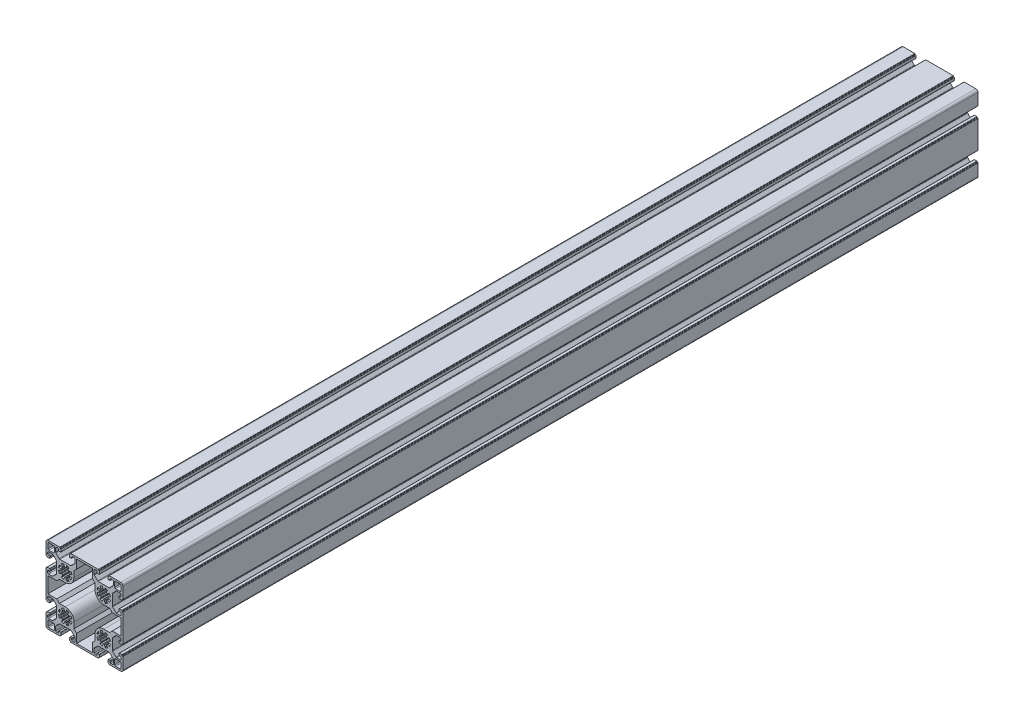
SolidWorks part; units mm, degrees
material "6063 T5"
ref_plane "Спереди" through (0, 0, 0) normal (0, 0, 1) x (1, 0, 0)
ref_plane "Сверху" through (0, 0, 0) normal (0, 1, 0) x (1, 0, 0)
ref_plane "Справа" through (0, 0, 0) normal (1, 0, 0) x (0, 0, -1)
sketch "Эскиз1" plane through (0, 0, 0) normal (0, 0, 1) x (1, 0, 0)
  line L0 (-19.98, 20.5457) -> (20.02, 20.5457) construction
  line L1 (-22.5, 11.25) -> (-22.5, 20)
  line L2 (-20, 22.5) -> (-11.25, 22.5)
  line L3 (65.3, 14) -> (65.3, 19.5)
  line L4 (-13.8, 13) -> (-19.3, 13)
  line L5 (-12.8, 14) -> (-12.8, 19.5)
  line L6 (-13.8, 20.5) -> (-19.3, 20.5)
  line L7 (-20.3, 14) -> (-20.3, 19.5)
  line L8 (0, 0) -> (22.5, 0) construction
  line L13 (0, 0) -> (0, -22.5) construction
  line L14 (0, -22.5) -> (22.5, -22.5) construction
  line L19 (22.5, 0) -> (22.5, -22.5) construction
  line L25 (58.8, 20.5) -> (64.3, 20.5)
  line L26 (-22.5383, 27.0237) -> (22.4617, 27.0237) construction
  line L27 (57.8, 14) -> (57.8, 19.5)
  line L28 (58.8, 13) -> (64.3, 13)
  line L29 (65, 22.5) -> (56.25, 22.5)
  line L30 (67.5, 11.25) -> (67.5, 20)
  line L31 (0, -45) -> (22.5, -45) construction
  line L32 (67.5, -56.25) -> (67.5, -65)
  line L33 (65, -67.5) -> (56.25, -67.5)
  line L34 (58.8, -58) -> (64.3, -58)
  line L35 (57.8, -59) -> (57.8, -64.5)
  line L36 (58.8, -65.5) -> (64.3, -65.5)
  line L37 (-20.3, -59) -> (-20.3, -64.5)
  line L38 (-13.8, -65.5) -> (-19.3, -65.5)
  line L42 (-12.8, -59) -> (-12.8, -64.5)
  line L47 (-13.8, -58) -> (-19.3, -58)
  line L48 (65.3, -59) -> (65.3, -64.5)
  line L49 (-20, -67.5) -> (-11.25, -67.5)
  line L50 (-31.9726, 22.6581) -> (-31.9726, -67.3419) construction
  line L51 (-22.5, -56.25) -> (-22.5, -65)
  line L52 (-22.5, -11.25) -> (-22.5, -33.75)
  line L53 (67.5, -11.25) -> (67.5, -33.75)
  line L55 (11.25, 22.5) -> (33.75, 22.5)
  line L57 (11.25, -67.5) -> (33.75, -67.5)
  line L59 (-22.4849, 32.3089) -> (67.5151, 32.3089) construction
  line L60 (22.5, -22.5) -> (0, 0) construction
  line L61 (-20.3, -31.75) -> (-20.3, -13.25)
  line L62 (-20.3, -13.25) -> (-9.9118, -13.25)
  line L63 (-9.9118, -13.25) -> (-6.8618, -10.2)
  line L64 (-6.8618, -10.2) -> (0, -10.2)
  line L65 (10.2, 6.8618) -> (10.2, 0)
  line L66 (13.25, 9.9118) -> (10.2, 6.8618)
  line L67 (13.25, 20.3) -> (13.25, 9.9118)
  line L68 (31.75, 20.3) -> (13.25, 20.3)
  line L70 (-20.3, -31.75) -> (-9.9118, -31.75)
  line L71 (-9.9118, -31.75) -> (-6.8618, -34.8)
  line L72 (-6.8618, -34.8) -> (0, -34.8)
  line L73 (10.2, -51.8618) -> (10.2, -45)
  line L74 (13.25, -54.9118) -> (10.2, -51.8618)
  line L75 (13.25, -65.3) -> (13.25, -54.9118)
  line L76 (31.75, -65.3) -> (13.25, -65.3)
  line L77 (31.75, 20.3) -> (31.75, 9.9118)
  line L78 (31.75, 9.9118) -> (34.8, 6.8618)
  line L79 (34.8, 6.8618) -> (34.8, 0)
  line L80 (51.8618, -10.2) -> (45, -10.2)
  line L81 (54.9118, -13.25) -> (51.8618, -10.2)
  line L82 (65.3, -13.25) -> (54.9118, -13.25)
  line L83 (65.3, -31.75) -> (65.3, -13.25)
  line L84 (65.3, -31.75) -> (54.9118, -31.75)
  line L85 (54.9118, -31.75) -> (51.8618, -34.8)
  line L86 (51.8618, -34.8) -> (45, -34.8)
  line L87 (34.8, -51.8618) -> (34.8, -45)
  line L88 (31.75, -54.9118) -> (34.8, -51.8618)
  line L89 (31.75, -65.3) -> (31.75, -54.9118)
  arc A0 (-22.5, 20) -> (-20, 22.5) centre (-20, 20) cw
  arc A1 (-19.3, 20.5) -> (-20.3, 19.5) centre (-19.3, 19.5) ccw
  arc A2 (-19.3, 13) -> (-20.3, 14) centre (-19.3, 14) cw
  arc A3 (-13.8, 13) -> (-12.8, 14) centre (-13.8, 14) ccw
  arc A4 (-12.8, 19.5) -> (-13.8, 20.5) centre (-13.8, 19.5) ccw
  arc A5 (57.8, 19.5) -> (58.8, 20.5) centre (58.8, 19.5) cw
  arc A6 (58.8, 13) -> (57.8, 14) centre (58.8, 14) cw
  arc A7 (64.3, 13) -> (65.3, 14) centre (64.3, 14) ccw
  arc A8 (64.3, 20.5) -> (65.3, 19.5) centre (64.3, 19.5) cw
  arc A9 (67.5, 20) -> (65, 22.5) centre (65, 20) ccw
  arc A10 (67.5, -65) -> (65, -67.5) centre (65, -65) cw
  arc A11 (64.3, -65.5) -> (65.3, -64.5) centre (64.3, -64.5) ccw
  arc A12 (64.3, -58) -> (65.3, -59) centre (64.3, -59) cw
  arc A13 (58.8, -58) -> (57.8, -59) centre (58.8, -59) ccw
  arc A14 (57.8, -64.5) -> (58.8, -65.5) centre (58.8, -64.5) ccw
  arc A15 (-12.8, -64.5) -> (-13.8, -65.5) centre (-13.8, -64.5) cw
  arc A16 (-13.8, -58) -> (-12.8, -59) centre (-13.8, -59) cw
  arc A17 (-19.3, -58) -> (-20.3, -59) centre (-19.3, -59) ccw
  arc A18 (-19.3, -65.5) -> (-20.3, -64.5) centre (-19.3, -64.5) cw
  arc A19 (-22.5, -65) -> (-20, -67.5) centre (-20, -65) ccw
  arc A20 (0, -10.2) -> (10.2, 0) centre (0, 0) ccw
  arc A21 (0, -34.8) -> (10.2, -45) centre (0, -45) cw
  arc A22 (45, -10.2) -> (34.8, 0) centre (45, 0) cw
  arc A23 (45, -34.8) -> (34.8, -45) centre (45, -45) ccw
  point P5 (0, 0)
  point P43 (45, 0)
  point P81 (45, -45)
  point P82 (0, -45)
  point P107 (-20.3, -22.5)
  point P120 (22.5, 20.3)
  point P131 (22.5, -65.3)
  line B0 (-22.5, 11.25) -> (-22.5, 6.4)
  line B1 (-22.2, 6.1) -> (-21.8, 6.1)
  line B2 (-21.5, 5.8) -> (-21.5, 5.4)
  line B3 (-21.2, 5.1) -> (-18.3, 5.1)
  line B4 (-18, 5.4) -> (-18, 7.3)
  line B5 (-18.3, 7.6) -> (-19.5, 7.6)
  line B6 (-20.5, 8.6) -> (-20.5, 10.25)
  line B7 (-19.5, 11.25) -> (-15.1142, 11.25)
  line B8 (-14.4071, 10.9571) -> (-10.4929, 7.0429)
  line B9 (-10.2, 6.3358) -> (-10.2, -6.3358)
  line B10 (-10.2, 0) -> (-22.5, 0) construction
  line B11 (-14.4071, -10.9571) -> (-10.4929, -7.0429)
  line B12 (-19.5, -11.25) -> (-15.1142, -11.25)
  line B13 (-20.5, -8.6) -> (-20.5, -10.25)
  line B14 (-18.3, -7.6) -> (-19.5, -7.6)
  line B15 (-18, -5.4) -> (-18, -7.3)
  line B16 (-21.2, -5.1) -> (-18.3, -5.1)
  line B17 (-21.5, -5.8) -> (-21.5, -5.4)
  line B18 (-22.2, -6.1) -> (-21.8, -6.1)
  line B19 (-22.5, -11.25) -> (-22.5, -6.4)
  arc B20 (-18, 7.3) -> (-18.3, 7.6) centre (-18.3, 7.3) ccw
  arc B21 (-18.3, 5.1) -> (-18, 5.4) centre (-18.3, 5.4) ccw
  arc B22 (-21.5, 5.4) -> (-21.2, 5.1) centre (-21.2, 5.4) ccw
  arc B23 (-21.8, 6.1) -> (-21.5, 5.8) centre (-21.8, 5.8) cw
  arc B24 (-22.5, 6.4) -> (-22.2, 6.1) centre (-22.2, 6.4) ccw
  arc B25 (-10.4929, 7.0429) -> (-10.2, 6.3358) centre (-11.2, 6.3358) cw
  arc B26 (-15.1142, 11.25) -> (-14.4071, 10.9571) centre (-15.1142, 10.25) cw
  arc B27 (-20.5, 10.25) -> (-19.5, 11.25) centre (-19.5, 10.25) cw
  arc B28 (-19.5, 7.6) -> (-20.5, 8.6) centre (-19.5, 8.6) cw
  arc B29 (-19.5, -7.6) -> (-20.5, -8.6) centre (-19.5, -8.6) ccw
  arc B30 (-20.5, -10.25) -> (-19.5, -11.25) centre (-19.5, -10.25) ccw
  arc B31 (-15.1142, -11.25) -> (-14.4071, -10.9571) centre (-15.1142, -10.25) ccw
  arc B32 (-10.4929, -7.0429) -> (-10.2, -6.3358) centre (-11.2, -6.3358) ccw
  arc B33 (-22.5, -6.4) -> (-22.2, -6.1) centre (-22.2, -6.4) cw
  arc B34 (-21.8, -6.1) -> (-21.5, -5.8) centre (-21.8, -5.8) ccw
  arc B35 (-21.5, -5.4) -> (-21.2, -5.1) centre (-21.2, -5.4) cw
  arc B36 (-18.3, -5.1) -> (-18, -5.4) centre (-18.3, -5.4) cw
  arc B37 (-18, -7.3) -> (-18.3, -7.6) centre (-18.3, -7.3) cw
  line B38 (0, 0) -> (3.6062, 3.6062) construction
  line B39 (1.3637, 7.358) -> (1.0164, 5.4842)
  line B40 (3.1592, 4.5967) -> (4.2386, 6.1672)
  line B41 (0, 0) -> (0, 5.1) construction
  arc B42 (0.478, -5.0776) -> (-0.478, -5.0776) centre (0, 0) cw
  arc B43 (-6.8804, -4.0816) -> (-7.7513, -1.979) centre (0, 0) cw
  arc B44 (3.9283, 3.2524) -> (3.2524, 3.9283) centre (0, 0) ccw
  arc B45 (4.0816, 6.8804) -> (1.979, 7.7513) centre (0, 0) ccw
  arc B46 (0.478, 5.0776) -> (-0.478, 5.0776) centre (0, 0) ccw
  line B47 (-1.3637, 7.358) -> (-1.0164, 5.4842)
  arc B48 (4.0816, -6.8804) -> (1.979, -7.7513) centre (0, 0) cw
  arc B49 (-3.9283, -3.2524) -> (-3.2524, -3.9283) centre (0, 0) ccw
  line B50 (-3.1592, -4.5967) -> (-4.2386, -6.1672)
  line B51 (0, 0) -> (6.3318, 0) construction
  line B52 (4.5967, 3.1592) -> (6.1672, 4.2386)
  line B53 (7.358, 1.3637) -> (5.4842, 1.0164)
  line B54 (-7.358, 1.3637) -> (-5.4842, 1.0164)
  line B55 (-4.5967, 3.1592) -> (-6.1672, 4.2386)
  line B56 (-3.1592, 4.5967) -> (-4.2386, 6.1672)
  line B57 (7.358, -1.3637) -> (5.4842, -1.0164)
  line B58 (4.5967, -3.1592) -> (6.1672, -4.2386)
  line B59 (3.1592, -4.5967) -> (4.2386, -6.1672)
  line B60 (1.3637, -7.358) -> (1.0164, -5.4842)
  line B61 (-1.3637, -7.358) -> (-1.0164, -5.4842)
  line B62 (-4.5967, -3.1592) -> (-6.1672, -4.2386)
  line B63 (-7.358, -1.3637) -> (-5.4842, -1.0164)
  arc B64 (5.0776, 0.478) -> (5.0776, -0.478) centre (0, 0) cw
  arc B65 (6.8804, 4.0816) -> (7.7513, 1.979) centre (0, 0) cw
  arc B66 (-5.0776, 0.478) -> (-5.0776, -0.478) centre (0, 0) ccw
  arc B67 (-6.8804, 4.0816) -> (-7.7513, 1.979) centre (0, 0) ccw
  arc B68 (-3.9283, 3.2524) -> (-3.2524, 3.9283) centre (0, 0) cw
  arc B69 (-4.0816, 6.8804) -> (-1.979, 7.7513) centre (0, 0) cw
  arc B70 (6.8804, -4.0816) -> (7.7513, -1.979) centre (0, 0) ccw
  arc B71 (3.9283, -3.2524) -> (3.2524, -3.9283) centre (0, 0) cw
  arc B72 (-4.0816, -6.8804) -> (-1.979, -7.7513) centre (0, 0) ccw
  arc B73 (5.0776, 0.478) -> (5.4842, 1.0164) centre (5.5754, 0.5248) cw
  arc B74 (5.4842, -1.0164) -> (5.0776, -0.478) centre (5.5754, -0.5248) cw
  arc B75 (7.7513, -1.979) -> (7.358, -1.3637) centre (7.2669, -1.8554) ccw
  arc B76 (6.8804, -4.0816) -> (6.1672, -4.2386) centre (6.4504, -3.8265) cw
  arc B77 (3.9283, -3.2524) -> (4.5967, -3.1592) centre (4.3135, -3.5713) cw
  arc B78 (3.2524, -3.9283) -> (3.1592, -4.5967) centre (3.5713, -4.3135) ccw
  arc B79 (4.0816, -6.8804) -> (4.2386, -6.1672) centre (3.8265, -6.4504) ccw
  arc B80 (1.979, -7.7513) -> (1.3637, -7.358) centre (1.8554, -7.2669) cw
  arc B81 (0.478, -5.0776) -> (1.0164, -5.4842) centre (0.5248, -5.5754) cw
  arc B82 (-0.478, -5.0776) -> (-1.0164, -5.4842) centre (-0.5248, -5.5754) ccw
  arc B83 (-1.979, -7.7513) -> (-1.3637, -7.358) centre (-1.8554, -7.2669) ccw
  arc B84 (-4.0816, -6.8804) -> (-4.2386, -6.1672) centre (-3.8265, -6.4504) cw
  arc B85 (-3.2524, -3.9283) -> (-3.1592, -4.5967) centre (-3.5713, -4.3135) cw
  arc B86 (-3.9283, -3.2524) -> (-4.5967, -3.1592) centre (-4.3135, -3.5713) ccw
  arc B87 (-6.8804, -4.0816) -> (-6.1672, -4.2386) centre (-6.4504, -3.8265) ccw
  arc B88 (-7.7513, -1.979) -> (-7.358, -1.3637) centre (-7.2669, -1.8554) cw
  arc B89 (-5.4842, -1.0164) -> (-5.0776, -0.478) centre (-5.5754, -0.5248) ccw
  arc B90 (-5.0776, 0.478) -> (-5.4842, 1.0164) centre (-5.5754, 0.5248) ccw
  arc B91 (-7.7513, 1.979) -> (-7.358, 1.3637) centre (-7.2669, 1.8554) ccw
  arc B92 (-6.8804, 4.0816) -> (-6.1672, 4.2386) centre (-6.4504, 3.8265) cw
  arc B93 (-3.9283, 3.2524) -> (-4.5967, 3.1592) centre (-4.3135, 3.5713) cw
  arc B94 (-3.2524, 3.9283) -> (-3.1592, 4.5967) centre (-3.5713, 4.3135) ccw
  arc B95 (-4.0816, 6.8804) -> (-4.2386, 6.1672) centre (-3.8265, 6.4504) ccw
  arc B96 (-1.979, 7.7513) -> (-1.3637, 7.358) centre (-1.8554, 7.2669) cw
  arc B97 (-1.0164, 5.4842) -> (-0.478, 5.0776) centre (-0.5248, 5.5754) ccw
  arc B98 (1.0164, 5.4842) -> (0.478, 5.0776) centre (0.5248, 5.5754) cw
  arc B99 (1.3637, 7.358) -> (1.979, 7.7513) centre (1.8554, 7.2669) cw
  arc B100 (4.2386, 6.1672) -> (4.0816, 6.8804) centre (3.8265, 6.4504) ccw
  arc B101 (3.1592, 4.5967) -> (3.2524, 3.9283) centre (3.5713, 4.3135) ccw
  arc B102 (4.5967, 3.1592) -> (3.9283, 3.2524) centre (4.3135, 3.5713) cw
  arc B103 (6.1672, 4.2386) -> (6.8804, 4.0816) centre (6.4504, 3.8265) cw
  arc B104 (7.7513, 1.979) -> (7.358, 1.3637) centre (7.2669, 1.8554) cw
  line B105 (11.25, 22.5) -> (6.4, 22.5)
  line B106 (6.1, 22.2) -> (6.1, 21.8)
  line B107 (5.8, 21.5) -> (5.4, 21.5)
  line B108 (5.1, 21.2) -> (5.1, 18.3)
  line B109 (5.4, 18) -> (7.3, 18)
  line B110 (7.6, 18.3) -> (7.6, 19.5)
  line B111 (8.6, 20.5) -> (10.25, 20.5)
  line B112 (11.25, 19.5) -> (11.25, 15.1142)
  line B113 (10.9571, 14.4071) -> (7.0429, 10.4929)
  line B114 (6.3358, 10.2) -> (-6.3358, 10.2)
  line B115 (0, 10.2) -> (0, 22.5) construction
  line B116 (-10.9571, 14.4071) -> (-7.0429, 10.4929)
  line B117 (-11.25, 19.5) -> (-11.25, 15.1142)
  line B118 (-8.6, 20.5) -> (-10.25, 20.5)
  line B119 (-7.6, 18.3) -> (-7.6, 19.5)
  line B120 (-5.4, 18) -> (-7.3, 18)
  line B121 (-5.1, 21.2) -> (-5.1, 18.3)
  line B122 (-5.8, 21.5) -> (-5.4, 21.5)
  line B123 (-6.1, 22.2) -> (-6.1, 21.8)
  line B124 (-11.25, 22.5) -> (-6.4, 22.5)
  arc B125 (7.3, 18) -> (7.6, 18.3) centre (7.3, 18.3) ccw
  arc B126 (5.1, 18.3) -> (5.4, 18) centre (5.4, 18.3) ccw
  arc B127 (5.4, 21.5) -> (5.1, 21.2) centre (5.4, 21.2) ccw
  arc B128 (6.1, 21.8) -> (5.8, 21.5) centre (5.8, 21.8) cw
  arc B129 (6.4, 22.5) -> (6.1, 22.2) centre (6.4, 22.2) ccw
  arc B130 (7.0429, 10.4929) -> (6.3358, 10.2) centre (6.3358, 11.2) cw
  arc B131 (11.25, 15.1142) -> (10.9571, 14.4071) centre (10.25, 15.1142) cw
  arc B132 (10.25, 20.5) -> (11.25, 19.5) centre (10.25, 19.5) cw
  arc B133 (7.6, 19.5) -> (8.6, 20.5) centre (8.6, 19.5) cw
  arc B134 (-7.6, 19.5) -> (-8.6, 20.5) centre (-8.6, 19.5) ccw
  arc B135 (-10.25, 20.5) -> (-11.25, 19.5) centre (-10.25, 19.5) ccw
  arc B136 (-11.25, 15.1142) -> (-10.9571, 14.4071) centre (-10.25, 15.1142) ccw
  arc B137 (-7.0429, 10.4929) -> (-6.3358, 10.2) centre (-6.3358, 11.2) ccw
  arc B138 (-6.4, 22.5) -> (-6.1, 22.2) centre (-6.4, 22.2) cw
  arc B139 (-6.1, 21.8) -> (-5.8, 21.5) centre (-5.8, 21.8) ccw
  arc B140 (-5.4, 21.5) -> (-5.1, 21.2) centre (-5.4, 21.2) cw
  arc B141 (-5.1, 18.3) -> (-5.4, 18) centre (-5.4, 18.3) cw
  arc B142 (-7.3, 18) -> (-7.6, 18.3) centre (-7.3, 18.3) cw
  line B143 (67.5, 11.25) -> (67.5, 6.4)
  line B144 (67.2, 6.1) -> (66.8, 6.1)
  line B145 (66.5, 5.8) -> (66.5, 5.4)
  line B146 (66.2, 5.1) -> (63.3, 5.1)
  line B147 (63, 5.4) -> (63, 7.3)
  line B148 (63.3, 7.6) -> (64.5, 7.6)
  line B149 (65.5, 8.6) -> (65.5, 10.25)
  line B150 (64.5, 11.25) -> (60.1142, 11.25)
  line B151 (59.4071, 10.9571) -> (55.4929, 7.0429)
  line B152 (55.2, 6.3358) -> (55.2, -6.3358)
  line B153 (55.2, 0) -> (67.5, 0) construction
  line B154 (59.4071, -10.9571) -> (55.4929, -7.0429)
  line B155 (64.5, -11.25) -> (60.1142, -11.25)
  line B156 (65.5, -8.6) -> (65.5, -10.25)
  line B157 (63.3, -7.6) -> (64.5, -7.6)
  line B158 (63, -5.4) -> (63, -7.3)
  line B159 (66.2, -5.1) -> (63.3, -5.1)
  line B160 (66.5, -5.8) -> (66.5, -5.4)
  line B161 (67.2, -6.1) -> (66.8, -6.1)
  line B162 (67.5, -11.25) -> (67.5, -6.4)
  arc B163 (63, 7.3) -> (63.3, 7.6) centre (63.3, 7.3) cw
  arc B164 (63.3, 5.1) -> (63, 5.4) centre (63.3, 5.4) cw
  arc B165 (66.5, 5.4) -> (66.2, 5.1) centre (66.2, 5.4) cw
  arc B166 (66.8, 6.1) -> (66.5, 5.8) centre (66.8, 5.8) ccw
  arc B167 (67.5, 6.4) -> (67.2, 6.1) centre (67.2, 6.4) cw
  arc B168 (55.4929, 7.0429) -> (55.2, 6.3358) centre (56.2, 6.3358) ccw
  arc B169 (60.1142, 11.25) -> (59.4071, 10.9571) centre (60.1142, 10.25) ccw
  arc B170 (65.5, 10.25) -> (64.5, 11.25) centre (64.5, 10.25) ccw
  arc B171 (64.5, 7.6) -> (65.5, 8.6) centre (64.5, 8.6) ccw
  arc B172 (64.5, -7.6) -> (65.5, -8.6) centre (64.5, -8.6) cw
  arc B173 (65.5, -10.25) -> (64.5, -11.25) centre (64.5, -10.25) cw
  arc B174 (60.1142, -11.25) -> (59.4071, -10.9571) centre (60.1142, -10.25) cw
  arc B175 (55.4929, -7.0429) -> (55.2, -6.3358) centre (56.2, -6.3358) cw
  arc B176 (67.5, -6.4) -> (67.2, -6.1) centre (67.2, -6.4) ccw
  arc B177 (66.8, -6.1) -> (66.5, -5.8) centre (66.8, -5.8) cw
  arc B178 (66.5, -5.4) -> (66.2, -5.1) centre (66.2, -5.4) ccw
  arc B179 (63.3, -5.1) -> (63, -5.4) centre (63.3, -5.4) ccw
  arc B180 (63, -7.3) -> (63.3, -7.6) centre (63.3, -7.3) ccw
  line B181 (45, 0) -> (41.3938, 3.6062) construction
  line B182 (43.6363, 7.358) -> (43.9836, 5.4842)
  line B183 (41.8408, 4.5967) -> (40.7614, 6.1672)
  line B184 (45, 0) -> (45, 5.1) construction
  arc B185 (44.522, -5.0776) -> (45.478, -5.0776) centre (45, 0) ccw
  arc B186 (51.8804, -4.0816) -> (52.7513, -1.979) centre (45, 0) ccw
  arc B187 (41.0717, 3.2524) -> (41.7476, 3.9283) centre (45, 0) cw
  arc B188 (40.9184, 6.8804) -> (43.021, 7.7513) centre (45, 0) cw
  arc B189 (44.522, 5.0776) -> (45.478, 5.0776) centre (45, 0) cw
  line B190 (46.3637, 7.358) -> (46.0164, 5.4842)
  arc B191 (40.9184, -6.8804) -> (43.021, -7.7513) centre (45, 0) ccw
  arc B192 (48.9283, -3.2524) -> (48.2524, -3.9283) centre (45, 0) cw
  line B193 (48.1592, -4.5967) -> (49.2386, -6.1672)
  line B194 (45, 0) -> (38.6682, 0) construction
  line B195 (40.4033, 3.1592) -> (38.8328, 4.2386)
  line B196 (37.642, 1.3637) -> (39.5158, 1.0164)
  line B197 (52.358, 1.3637) -> (50.4842, 1.0164)
  line B198 (49.5967, 3.1592) -> (51.1672, 4.2386)
  line B199 (48.1592, 4.5967) -> (49.2386, 6.1672)
  line B200 (37.642, -1.3637) -> (39.5158, -1.0164)
  line B201 (40.4033, -3.1592) -> (38.8328, -4.2386)
  line B202 (41.8408, -4.5967) -> (40.7614, -6.1672)
  line B203 (43.6363, -7.358) -> (43.9836, -5.4842)
  line B204 (46.3637, -7.358) -> (46.0164, -5.4842)
  line B205 (49.5967, -3.1592) -> (51.1672, -4.2386)
  line B206 (52.358, -1.3637) -> (50.4842, -1.0164)
  arc B207 (39.9224, 0.478) -> (39.9224, -0.478) centre (45, 0) ccw
  arc B208 (38.1196, 4.0816) -> (37.2487, 1.979) centre (45, 0) ccw
  arc B209 (50.0776, 0.478) -> (50.0776, -0.478) centre (45, 0) cw
  arc B210 (51.8804, 4.0816) -> (52.7513, 1.979) centre (45, 0) cw
  arc B211 (48.9283, 3.2524) -> (48.2524, 3.9283) centre (45, 0) ccw
  arc B212 (49.0816, 6.8804) -> (46.979, 7.7513) centre (45, 0) ccw
  arc B213 (38.1196, -4.0816) -> (37.2487, -1.979) centre (45, 0) cw
  arc B214 (41.0717, -3.2524) -> (41.7476, -3.9283) centre (45, 0) ccw
  arc B215 (49.0816, -6.8804) -> (46.979, -7.7513) centre (45, 0) cw
  arc B216 (39.9224, 0.478) -> (39.5158, 1.0164) centre (39.4246, 0.5248) ccw
  arc B217 (39.5158, -1.0164) -> (39.9224, -0.478) centre (39.4246, -0.5248) ccw
  arc B218 (37.2487, -1.979) -> (37.642, -1.3637) centre (37.7331, -1.8554) cw
  arc B219 (38.1196, -4.0816) -> (38.8328, -4.2386) centre (38.5496, -3.8265) ccw
  arc B220 (41.0717, -3.2524) -> (40.4033, -3.1592) centre (40.6865, -3.5713) ccw
  arc B221 (41.7476, -3.9283) -> (41.8408, -4.5967) centre (41.4287, -4.3135) cw
  arc B222 (40.9184, -6.8804) -> (40.7614, -6.1672) centre (41.1735, -6.4504) cw
  arc B223 (43.021, -7.7513) -> (43.6363, -7.358) centre (43.1446, -7.2669) ccw
  arc B224 (44.522, -5.0776) -> (43.9836, -5.4842) centre (44.4752, -5.5754) ccw
  arc B225 (45.478, -5.0776) -> (46.0164, -5.4842) centre (45.5248, -5.5754) cw
  arc B226 (46.979, -7.7513) -> (46.3637, -7.358) centre (46.8554, -7.2669) cw
  arc B227 (49.0816, -6.8804) -> (49.2386, -6.1672) centre (48.8265, -6.4504) ccw
  arc B228 (48.2524, -3.9283) -> (48.1592, -4.5967) centre (48.5713, -4.3135) ccw
  arc B229 (48.9283, -3.2524) -> (49.5967, -3.1592) centre (49.3135, -3.5713) cw
  arc B230 (51.8804, -4.0816) -> (51.1672, -4.2386) centre (51.4504, -3.8265) cw
  arc B231 (52.7513, -1.979) -> (52.358, -1.3637) centre (52.2669, -1.8554) ccw
  arc B232 (50.4842, -1.0164) -> (50.0776, -0.478) centre (50.5754, -0.5248) cw
  arc B233 (50.0776, 0.478) -> (50.4842, 1.0164) centre (50.5754, 0.5248) cw
  arc B234 (52.7513, 1.979) -> (52.358, 1.3637) centre (52.2669, 1.8554) cw
  arc B235 (51.8804, 4.0816) -> (51.1672, 4.2386) centre (51.4504, 3.8265) ccw
  arc B236 (48.9283, 3.2524) -> (49.5967, 3.1592) centre (49.3135, 3.5713) ccw
  arc B237 (48.2524, 3.9283) -> (48.1592, 4.5967) centre (48.5713, 4.3135) cw
  arc B238 (49.0816, 6.8804) -> (49.2386, 6.1672) centre (48.8265, 6.4504) cw
  arc B239 (46.979, 7.7513) -> (46.3637, 7.358) centre (46.8554, 7.2669) ccw
  arc B240 (46.0164, 5.4842) -> (45.478, 5.0776) centre (45.5248, 5.5754) cw
  arc B241 (43.9836, 5.4842) -> (44.522, 5.0776) centre (44.4752, 5.5754) ccw
  arc B242 (43.6363, 7.358) -> (43.021, 7.7513) centre (43.1446, 7.2669) ccw
  arc B243 (40.7614, 6.1672) -> (40.9184, 6.8804) centre (41.1735, 6.4504) cw
  arc B244 (41.8408, 4.5967) -> (41.7476, 3.9283) centre (41.4287, 4.3135) cw
  arc B245 (40.4033, 3.1592) -> (41.0717, 3.2524) centre (40.6865, 3.5713) ccw
  arc B246 (38.8328, 4.2386) -> (38.1196, 4.0816) centre (38.5496, 3.8265) ccw
  arc B247 (37.2487, 1.979) -> (37.642, 1.3637) centre (37.7331, 1.8554) ccw
  line B248 (33.75, 22.5) -> (38.6, 22.5)
  line B249 (38.9, 22.2) -> (38.9, 21.8)
  line B250 (39.2, 21.5) -> (39.6, 21.5)
  line B251 (39.9, 21.2) -> (39.9, 18.3)
  line B252 (39.6, 18) -> (37.7, 18)
  line B253 (37.4, 18.3) -> (37.4, 19.5)
  line B254 (36.4, 20.5) -> (34.75, 20.5)
  line B255 (33.75, 19.5) -> (33.75, 15.1142)
  line B256 (34.0429, 14.4071) -> (37.9571, 10.4929)
  line B257 (38.6642, 10.2) -> (51.3358, 10.2)
  line B258 (45, 10.2) -> (45, 22.5) construction
  line B259 (55.9571, 14.4071) -> (52.0429, 10.4929)
  line B260 (56.25, 19.5) -> (56.25, 15.1142)
  line B261 (53.6, 20.5) -> (55.25, 20.5)
  line B262 (52.6, 18.3) -> (52.6, 19.5)
  line B263 (50.4, 18) -> (52.3, 18)
  line B264 (50.1, 21.2) -> (50.1, 18.3)
  line B265 (50.8, 21.5) -> (50.4, 21.5)
  line B266 (51.1, 22.2) -> (51.1, 21.8)
  line B267 (56.25, 22.5) -> (51.4, 22.5)
  arc B268 (37.7, 18) -> (37.4, 18.3) centre (37.7, 18.3) cw
  arc B269 (39.9, 18.3) -> (39.6, 18) centre (39.6, 18.3) cw
  arc B270 (39.6, 21.5) -> (39.9, 21.2) centre (39.6, 21.2) cw
  arc B271 (38.9, 21.8) -> (39.2, 21.5) centre (39.2, 21.8) ccw
  arc B272 (38.6, 22.5) -> (38.9, 22.2) centre (38.6, 22.2) cw
  arc B273 (37.9571, 10.4929) -> (38.6642, 10.2) centre (38.6642, 11.2) ccw
  arc B274 (33.75, 15.1142) -> (34.0429, 14.4071) centre (34.75, 15.1142) ccw
  arc B275 (34.75, 20.5) -> (33.75, 19.5) centre (34.75, 19.5) ccw
  arc B276 (37.4, 19.5) -> (36.4, 20.5) centre (36.4, 19.5) ccw
  arc B277 (52.6, 19.5) -> (53.6, 20.5) centre (53.6, 19.5) cw
  arc B278 (55.25, 20.5) -> (56.25, 19.5) centre (55.25, 19.5) cw
  arc B279 (56.25, 15.1142) -> (55.9571, 14.4071) centre (55.25, 15.1142) cw
  arc B280 (52.0429, 10.4929) -> (51.3358, 10.2) centre (51.3358, 11.2) cw
  arc B281 (51.4, 22.5) -> (51.1, 22.2) centre (51.4, 22.2) ccw
  arc B282 (51.1, 21.8) -> (50.8, 21.5) centre (50.8, 21.8) cw
  arc B283 (50.4, 21.5) -> (50.1, 21.2) centre (50.4, 21.2) ccw
  arc B284 (50.1, 18.3) -> (50.4, 18) centre (50.4, 18.3) ccw
  arc B285 (52.3, 18) -> (52.6, 18.3) centre (52.3, 18.3) ccw
  line B286 (-22.5, -56.25) -> (-22.5, -51.4)
  line B287 (-22.2, -51.1) -> (-21.8, -51.1)
  line B288 (-21.5, -50.8) -> (-21.5, -50.4)
  line B289 (-21.2, -50.1) -> (-18.3, -50.1)
  line B290 (-18, -50.4) -> (-18, -52.3)
  line B291 (-18.3, -52.6) -> (-19.5, -52.6)
  line B292 (-20.5, -53.6) -> (-20.5, -55.25)
  line B293 (-19.5, -56.25) -> (-15.1142, -56.25)
  line B294 (-14.4071, -55.9571) -> (-10.4929, -52.0429)
  line B295 (-10.2, -51.3358) -> (-10.2, -38.6642)
  line B296 (-10.2, -45) -> (-22.5, -45) construction
  line B297 (-14.4071, -34.0429) -> (-10.4929, -37.9571)
  line B298 (-19.5, -33.75) -> (-15.1142, -33.75)
  line B299 (-20.5, -36.4) -> (-20.5, -34.75)
  line B300 (-18.3, -37.4) -> (-19.5, -37.4)
  line B301 (-18, -39.6) -> (-18, -37.7)
  line B302 (-21.2, -39.9) -> (-18.3, -39.9)
  line B303 (-21.5, -39.2) -> (-21.5, -39.6)
  line B304 (-22.2, -38.9) -> (-21.8, -38.9)
  line B305 (-22.5, -33.75) -> (-22.5, -38.6)
  arc B306 (-18, -52.3) -> (-18.3, -52.6) centre (-18.3, -52.3) cw
  arc B307 (-18.3, -50.1) -> (-18, -50.4) centre (-18.3, -50.4) cw
  arc B308 (-21.5, -50.4) -> (-21.2, -50.1) centre (-21.2, -50.4) cw
  arc B309 (-21.8, -51.1) -> (-21.5, -50.8) centre (-21.8, -50.8) ccw
  arc B310 (-22.5, -51.4) -> (-22.2, -51.1) centre (-22.2, -51.4) cw
  arc B311 (-10.4929, -52.0429) -> (-10.2, -51.3358) centre (-11.2, -51.3358) ccw
  arc B312 (-15.1142, -56.25) -> (-14.4071, -55.9571) centre (-15.1142, -55.25) ccw
  arc B313 (-20.5, -55.25) -> (-19.5, -56.25) centre (-19.5, -55.25) ccw
  arc B314 (-19.5, -52.6) -> (-20.5, -53.6) centre (-19.5, -53.6) ccw
  arc B315 (-19.5, -37.4) -> (-20.5, -36.4) centre (-19.5, -36.4) cw
  arc B316 (-20.5, -34.75) -> (-19.5, -33.75) centre (-19.5, -34.75) cw
  arc B317 (-15.1142, -33.75) -> (-14.4071, -34.0429) centre (-15.1142, -34.75) cw
  arc B318 (-10.4929, -37.9571) -> (-10.2, -38.6642) centre (-11.2, -38.6642) cw
  arc B319 (-22.5, -38.6) -> (-22.2, -38.9) centre (-22.2, -38.6) ccw
  arc B320 (-21.8, -38.9) -> (-21.5, -39.2) centre (-21.8, -39.2) cw
  arc B321 (-21.5, -39.6) -> (-21.2, -39.9) centre (-21.2, -39.6) ccw
  arc B322 (-18.3, -39.9) -> (-18, -39.6) centre (-18.3, -39.6) ccw
  arc B323 (-18, -37.7) -> (-18.3, -37.4) centre (-18.3, -37.7) ccw
  line B324 (0, -45) -> (3.6062, -48.6062) construction
  line B325 (1.3637, -52.358) -> (1.0164, -50.4842)
  line B326 (3.1592, -49.5967) -> (4.2386, -51.1672)
  line B327 (0, -45) -> (0, -50.1) construction
  arc B328 (0.478, -39.9224) -> (-0.478, -39.9224) centre (0, -45) ccw
  arc B329 (-6.8804, -40.9184) -> (-7.7513, -43.021) centre (0, -45) ccw
  arc B330 (3.9283, -48.2524) -> (3.2524, -48.9283) centre (0, -45) cw
  arc B331 (4.0816, -51.8804) -> (1.979, -52.7513) centre (0, -45) cw
  arc B332 (0.478, -50.0776) -> (-0.478, -50.0776) centre (0, -45) cw
  line B333 (-1.3637, -52.358) -> (-1.0164, -50.4842)
  arc B334 (4.0816, -38.1196) -> (1.979, -37.2487) centre (0, -45) ccw
  arc B335 (-3.9283, -41.7476) -> (-3.2524, -41.0717) centre (0, -45) cw
  line B336 (-3.1592, -40.4033) -> (-4.2386, -38.8328)
  line B337 (0, -45) -> (6.3318, -45) construction
  line B338 (4.5967, -48.1592) -> (6.1672, -49.2386)
  line B339 (7.358, -46.3637) -> (5.4842, -46.0164)
  line B340 (-7.358, -46.3637) -> (-5.4842, -46.0164)
  line B341 (-4.5967, -48.1592) -> (-6.1672, -49.2386)
  line B342 (-3.1592, -49.5967) -> (-4.2386, -51.1672)
  line B343 (7.358, -43.6363) -> (5.4842, -43.9836)
  line B344 (4.5967, -41.8408) -> (6.1672, -40.7614)
  line B345 (3.1592, -40.4033) -> (4.2386, -38.8328)
  line B346 (1.3637, -37.642) -> (1.0164, -39.5158)
  line B347 (-1.3637, -37.642) -> (-1.0164, -39.5158)
  line B348 (-4.5967, -41.8408) -> (-6.1672, -40.7614)
  line B349 (-7.358, -43.6363) -> (-5.4842, -43.9836)
  arc B350 (5.0776, -45.478) -> (5.0776, -44.522) centre (0, -45) ccw
  arc B351 (6.8804, -49.0816) -> (7.7513, -46.979) centre (0, -45) ccw
  arc B352 (-5.0776, -45.478) -> (-5.0776, -44.522) centre (0, -45) cw
  arc B353 (-6.8804, -49.0816) -> (-7.7513, -46.979) centre (0, -45) cw
  arc B354 (-3.9283, -48.2524) -> (-3.2524, -48.9283) centre (0, -45) ccw
  arc B355 (-4.0816, -51.8804) -> (-1.979, -52.7513) centre (0, -45) ccw
  arc B356 (6.8804, -40.9184) -> (7.7513, -43.021) centre (0, -45) cw
  arc B357 (3.9283, -41.7476) -> (3.2524, -41.0717) centre (0, -45) ccw
  arc B358 (-4.0816, -38.1196) -> (-1.979, -37.2487) centre (0, -45) cw
  arc B359 (5.0776, -45.478) -> (5.4842, -46.0164) centre (5.5754, -45.5248) ccw
  arc B360 (5.4842, -43.9836) -> (5.0776, -44.522) centre (5.5754, -44.4752) ccw
  arc B361 (7.7513, -43.021) -> (7.358, -43.6363) centre (7.2669, -43.1446) cw
  arc B362 (6.8804, -40.9184) -> (6.1672, -40.7614) centre (6.4504, -41.1735) ccw
  arc B363 (3.9283, -41.7476) -> (4.5967, -41.8408) centre (4.3135, -41.4287) ccw
  arc B364 (3.2524, -41.0717) -> (3.1592, -40.4033) centre (3.5713, -40.6865) cw
  arc B365 (4.0816, -38.1196) -> (4.2386, -38.8328) centre (3.8265, -38.5496) cw
  arc B366 (1.979, -37.2487) -> (1.3637, -37.642) centre (1.8554, -37.7331) ccw
  arc B367 (0.478, -39.9224) -> (1.0164, -39.5158) centre (0.5248, -39.4246) ccw
  arc B368 (-0.478, -39.9224) -> (-1.0164, -39.5158) centre (-0.5248, -39.4246) cw
  arc B369 (-1.979, -37.2487) -> (-1.3637, -37.642) centre (-1.8554, -37.7331) cw
  arc B370 (-4.0816, -38.1196) -> (-4.2386, -38.8328) centre (-3.8265, -38.5496) ccw
  arc B371 (-3.2524, -41.0717) -> (-3.1592, -40.4033) centre (-3.5713, -40.6865) ccw
  arc B372 (-3.9283, -41.7476) -> (-4.5967, -41.8408) centre (-4.3135, -41.4287) cw
  arc B373 (-6.8804, -40.9184) -> (-6.1672, -40.7614) centre (-6.4504, -41.1735) cw
  arc B374 (-7.7513, -43.021) -> (-7.358, -43.6363) centre (-7.2669, -43.1446) ccw
  arc B375 (-5.4842, -43.9836) -> (-5.0776, -44.522) centre (-5.5754, -44.4752) cw
  arc B376 (-5.0776, -45.478) -> (-5.4842, -46.0164) centre (-5.5754, -45.5248) cw
  arc B377 (-7.7513, -46.979) -> (-7.358, -46.3637) centre (-7.2669, -46.8554) cw
  arc B378 (-6.8804, -49.0816) -> (-6.1672, -49.2386) centre (-6.4504, -48.8265) ccw
  arc B379 (-3.9283, -48.2524) -> (-4.5967, -48.1592) centre (-4.3135, -48.5713) ccw
  arc B380 (-3.2524, -48.9283) -> (-3.1592, -49.5967) centre (-3.5713, -49.3135) cw
  arc B381 (-4.0816, -51.8804) -> (-4.2386, -51.1672) centre (-3.8265, -51.4504) cw
  arc B382 (-1.979, -52.7513) -> (-1.3637, -52.358) centre (-1.8554, -52.2669) ccw
  arc B383 (-1.0164, -50.4842) -> (-0.478, -50.0776) centre (-0.5248, -50.5754) cw
  arc B384 (1.0164, -50.4842) -> (0.478, -50.0776) centre (0.5248, -50.5754) ccw
  arc B385 (1.3637, -52.358) -> (1.979, -52.7513) centre (1.8554, -52.2669) ccw
  arc B386 (4.2386, -51.1672) -> (4.0816, -51.8804) centre (3.8265, -51.4504) cw
  arc B387 (3.1592, -49.5967) -> (3.2524, -48.9283) centre (3.5713, -49.3135) cw
  arc B388 (4.5967, -48.1592) -> (3.9283, -48.2524) centre (4.3135, -48.5713) ccw
  arc B389 (6.1672, -49.2386) -> (6.8804, -49.0816) centre (6.4504, -48.8265) ccw
  arc B390 (7.7513, -46.979) -> (7.358, -46.3637) centre (7.2669, -46.8554) ccw
  line B391 (45, -45) -> (41.3938, -48.6062) construction
  line B392 (43.6363, -52.358) -> (43.9836, -50.4842)
  line B393 (41.8408, -49.5967) -> (40.7614, -51.1672)
  line B394 (45, -45) -> (45, -50.1) construction
  arc B395 (44.522, -39.9224) -> (45.478, -39.9224) centre (45, -45) cw
  arc B396 (51.8804, -40.9184) -> (52.7513, -43.021) centre (45, -45) cw
  arc B397 (41.0717, -48.2524) -> (41.7476, -48.9283) centre (45, -45) ccw
  arc B398 (40.9184, -51.8804) -> (43.021, -52.7513) centre (45, -45) ccw
  arc B399 (44.522, -50.0776) -> (45.478, -50.0776) centre (45, -45) ccw
  line B400 (46.3637, -52.358) -> (46.0164, -50.4842)
  arc B401 (40.9184, -38.1196) -> (43.021, -37.2487) centre (45, -45) cw
  arc B402 (48.9283, -41.7476) -> (48.2524, -41.0717) centre (45, -45) ccw
  line B403 (48.1592, -40.4033) -> (49.2386, -38.8328)
  line B404 (45, -45) -> (38.6682, -45) construction
  line B405 (40.4033, -48.1592) -> (38.8328, -49.2386)
  line B406 (37.642, -46.3637) -> (39.5158, -46.0164)
  line B407 (52.358, -46.3637) -> (50.4842, -46.0164)
  line B408 (49.5967, -48.1592) -> (51.1672, -49.2386)
  line B409 (48.1592, -49.5967) -> (49.2386, -51.1672)
  line B410 (37.642, -43.6363) -> (39.5158, -43.9836)
  line B411 (40.4033, -41.8408) -> (38.8328, -40.7614)
  line B412 (41.8408, -40.4033) -> (40.7614, -38.8328)
  line B413 (43.6363, -37.642) -> (43.9836, -39.5158)
  line B414 (46.3637, -37.642) -> (46.0164, -39.5158)
  line B415 (49.5967, -41.8408) -> (51.1672, -40.7614)
  line B416 (52.358, -43.6363) -> (50.4842, -43.9836)
  arc B417 (39.9224, -45.478) -> (39.9224, -44.522) centre (45, -45) cw
  arc B418 (38.1196, -49.0816) -> (37.2487, -46.979) centre (45, -45) cw
  arc B419 (50.0776, -45.478) -> (50.0776, -44.522) centre (45, -45) ccw
  arc B420 (51.8804, -49.0816) -> (52.7513, -46.979) centre (45, -45) ccw
  arc B421 (48.9283, -48.2524) -> (48.2524, -48.9283) centre (45, -45) cw
  arc B422 (49.0816, -51.8804) -> (46.979, -52.7513) centre (45, -45) cw
  arc B423 (38.1196, -40.9184) -> (37.2487, -43.021) centre (45, -45) ccw
  arc B424 (41.0717, -41.7476) -> (41.7476, -41.0717) centre (45, -45) cw
  arc B425 (49.0816, -38.1196) -> (46.979, -37.2487) centre (45, -45) ccw
  arc B426 (39.9224, -45.478) -> (39.5158, -46.0164) centre (39.4246, -45.5248) cw
  arc B427 (39.5158, -43.9836) -> (39.9224, -44.522) centre (39.4246, -44.4752) cw
  arc B428 (37.2487, -43.021) -> (37.642, -43.6363) centre (37.7331, -43.1446) ccw
  arc B429 (38.1196, -40.9184) -> (38.8328, -40.7614) centre (38.5496, -41.1735) cw
  arc B430 (41.0717, -41.7476) -> (40.4033, -41.8408) centre (40.6865, -41.4287) cw
  arc B431 (41.7476, -41.0717) -> (41.8408, -40.4033) centre (41.4287, -40.6865) ccw
  arc B432 (40.9184, -38.1196) -> (40.7614, -38.8328) centre (41.1735, -38.5496) ccw
  arc B433 (43.021, -37.2487) -> (43.6363, -37.642) centre (43.1446, -37.7331) cw
  arc B434 (44.522, -39.9224) -> (43.9836, -39.5158) centre (44.4752, -39.4246) cw
  arc B435 (45.478, -39.9224) -> (46.0164, -39.5158) centre (45.5248, -39.4246) ccw
  arc B436 (46.979, -37.2487) -> (46.3637, -37.642) centre (46.8554, -37.7331) ccw
  arc B437 (49.0816, -38.1196) -> (49.2386, -38.8328) centre (48.8265, -38.5496) cw
  arc B438 (48.2524, -41.0717) -> (48.1592, -40.4033) centre (48.5713, -40.6865) cw
  arc B439 (48.9283, -41.7476) -> (49.5967, -41.8408) centre (49.3135, -41.4287) ccw
  arc B440 (51.8804, -40.9184) -> (51.1672, -40.7614) centre (51.4504, -41.1735) ccw
  arc B441 (52.7513, -43.021) -> (52.358, -43.6363) centre (52.2669, -43.1446) cw
  arc B442 (50.4842, -43.9836) -> (50.0776, -44.522) centre (50.5754, -44.4752) ccw
  arc B443 (50.0776, -45.478) -> (50.4842, -46.0164) centre (50.5754, -45.5248) ccw
  arc B444 (52.7513, -46.979) -> (52.358, -46.3637) centre (52.2669, -46.8554) ccw
  arc B445 (51.8804, -49.0816) -> (51.1672, -49.2386) centre (51.4504, -48.8265) cw
  arc B446 (48.9283, -48.2524) -> (49.5967, -48.1592) centre (49.3135, -48.5713) cw
  arc B447 (48.2524, -48.9283) -> (48.1592, -49.5967) centre (48.5713, -49.3135) ccw
  arc B448 (49.0816, -51.8804) -> (49.2386, -51.1672) centre (48.8265, -51.4504) ccw
  arc B449 (46.979, -52.7513) -> (46.3637, -52.358) centre (46.8554, -52.2669) cw
  arc B450 (46.0164, -50.4842) -> (45.478, -50.0776) centre (45.5248, -50.5754) ccw
  arc B451 (43.9836, -50.4842) -> (44.522, -50.0776) centre (44.4752, -50.5754) cw
  arc B452 (43.6363, -52.358) -> (43.021, -52.7513) centre (43.1446, -52.2669) cw
  arc B453 (40.7614, -51.1672) -> (40.9184, -51.8804) centre (41.1735, -51.4504) ccw
  arc B454 (41.8408, -49.5967) -> (41.7476, -48.9283) centre (41.4287, -49.3135) ccw
  arc B455 (40.4033, -48.1592) -> (41.0717, -48.2524) centre (40.6865, -48.5713) cw
  arc B456 (38.8328, -49.2386) -> (38.1196, -49.0816) centre (38.5496, -48.8265) cw
  arc B457 (37.2487, -46.979) -> (37.642, -46.3637) centre (37.7331, -46.8554) cw
  line B458 (11.25, -67.5) -> (6.4, -67.5)
  line B459 (6.1, -67.2) -> (6.1, -66.8)
  line B460 (5.8, -66.5) -> (5.4, -66.5)
  line B461 (5.1, -66.2) -> (5.1, -63.3)
  line B462 (5.4, -63) -> (7.3, -63)
  line B463 (7.6, -63.3) -> (7.6, -64.5)
  line B464 (8.6, -65.5) -> (10.25, -65.5)
  line B465 (11.25, -64.5) -> (11.25, -60.1142)
  line B466 (10.9571, -59.4071) -> (7.0429, -55.4929)
  line B467 (6.3358, -55.2) -> (-6.3358, -55.2)
  line B468 (0, -55.2) -> (0, -67.5) construction
  line B469 (-10.9571, -59.4071) -> (-7.0429, -55.4929)
  line B470 (-11.25, -64.5) -> (-11.25, -60.1142)
  line B471 (-8.6, -65.5) -> (-10.25, -65.5)
  line B472 (-7.6, -63.3) -> (-7.6, -64.5)
  line B473 (-5.4, -63) -> (-7.3, -63)
  line B474 (-5.1, -66.2) -> (-5.1, -63.3)
  line B475 (-5.8, -66.5) -> (-5.4, -66.5)
  line B476 (-6.1, -67.2) -> (-6.1, -66.8)
  line B477 (-11.25, -67.5) -> (-6.4, -67.5)
  arc B478 (7.3, -63) -> (7.6, -63.3) centre (7.3, -63.3) cw
  arc B479 (5.1, -63.3) -> (5.4, -63) centre (5.4, -63.3) cw
  arc B480 (5.4, -66.5) -> (5.1, -66.2) centre (5.4, -66.2) cw
  arc B481 (6.1, -66.8) -> (5.8, -66.5) centre (5.8, -66.8) ccw
  arc B482 (6.4, -67.5) -> (6.1, -67.2) centre (6.4, -67.2) cw
  arc B483 (7.0429, -55.4929) -> (6.3358, -55.2) centre (6.3358, -56.2) ccw
  arc B484 (11.25, -60.1142) -> (10.9571, -59.4071) centre (10.25, -60.1142) ccw
  arc B485 (10.25, -65.5) -> (11.25, -64.5) centre (10.25, -64.5) ccw
  arc B486 (7.6, -64.5) -> (8.6, -65.5) centre (8.6, -64.5) ccw
  arc B487 (-7.6, -64.5) -> (-8.6, -65.5) centre (-8.6, -64.5) cw
  arc B488 (-10.25, -65.5) -> (-11.25, -64.5) centre (-10.25, -64.5) cw
  arc B489 (-11.25, -60.1142) -> (-10.9571, -59.4071) centre (-10.25, -60.1142) cw
  arc B490 (-7.0429, -55.4929) -> (-6.3358, -55.2) centre (-6.3358, -56.2) cw
  arc B491 (-6.4, -67.5) -> (-6.1, -67.2) centre (-6.4, -67.2) ccw
  arc B492 (-6.1, -66.8) -> (-5.8, -66.5) centre (-5.8, -66.8) cw
  arc B493 (-5.4, -66.5) -> (-5.1, -66.2) centre (-5.4, -66.2) ccw
  arc B494 (-5.1, -63.3) -> (-5.4, -63) centre (-5.4, -63.3) ccw
  arc B495 (-7.3, -63) -> (-7.6, -63.3) centre (-7.3, -63.3) ccw
  line B496 (67.5, -56.25) -> (67.5, -51.4)
  line B497 (67.2, -51.1) -> (66.8, -51.1)
  line B498 (66.5, -50.8) -> (66.5, -50.4)
  line B499 (66.2, -50.1) -> (63.3, -50.1)
  line B500 (63, -50.4) -> (63, -52.3)
  line B501 (63.3, -52.6) -> (64.5, -52.6)
  line B502 (65.5, -53.6) -> (65.5, -55.25)
  line B503 (64.5, -56.25) -> (60.1142, -56.25)
  line B504 (59.4071, -55.9571) -> (55.4929, -52.0429)
  line B505 (55.2, -51.3358) -> (55.2, -38.6642)
  line B506 (55.2, -45) -> (67.5, -45) construction
  line B507 (59.4071, -34.0429) -> (55.4929, -37.9571)
  line B508 (64.5, -33.75) -> (60.1142, -33.75)
  line B509 (65.5, -36.4) -> (65.5, -34.75)
  line B510 (63.3, -37.4) -> (64.5, -37.4)
  line B511 (63, -39.6) -> (63, -37.7)
  line B512 (66.2, -39.9) -> (63.3, -39.9)
  line B513 (66.5, -39.2) -> (66.5, -39.6)
  line B514 (67.2, -38.9) -> (66.8, -38.9)
  line B515 (67.5, -33.75) -> (67.5, -38.6)
  arc B516 (63, -52.3) -> (63.3, -52.6) centre (63.3, -52.3) ccw
  arc B517 (63.3, -50.1) -> (63, -50.4) centre (63.3, -50.4) ccw
  arc B518 (66.5, -50.4) -> (66.2, -50.1) centre (66.2, -50.4) ccw
  arc B519 (66.8, -51.1) -> (66.5, -50.8) centre (66.8, -50.8) cw
  arc B520 (67.5, -51.4) -> (67.2, -51.1) centre (67.2, -51.4) ccw
  arc B521 (55.4929, -52.0429) -> (55.2, -51.3358) centre (56.2, -51.3358) cw
  arc B522 (60.1142, -56.25) -> (59.4071, -55.9571) centre (60.1142, -55.25) cw
  arc B523 (65.5, -55.25) -> (64.5, -56.25) centre (64.5, -55.25) cw
  arc B524 (64.5, -52.6) -> (65.5, -53.6) centre (64.5, -53.6) cw
  arc B525 (64.5, -37.4) -> (65.5, -36.4) centre (64.5, -36.4) ccw
  arc B526 (65.5, -34.75) -> (64.5, -33.75) centre (64.5, -34.75) ccw
  arc B527 (60.1142, -33.75) -> (59.4071, -34.0429) centre (60.1142, -34.75) ccw
  arc B528 (55.4929, -37.9571) -> (55.2, -38.6642) centre (56.2, -38.6642) ccw
  arc B529 (67.5, -38.6) -> (67.2, -38.9) centre (67.2, -38.6) cw
  arc B530 (66.8, -38.9) -> (66.5, -39.2) centre (66.8, -39.2) ccw
  arc B531 (66.5, -39.6) -> (66.2, -39.9) centre (66.2, -39.6) cw
  arc B532 (63.3, -39.9) -> (63, -39.6) centre (63.3, -39.6) cw
  arc B533 (63, -37.7) -> (63.3, -37.4) centre (63.3, -37.7) cw
  line B534 (33.75, -67.5) -> (38.6, -67.5)
  line B535 (38.9, -67.2) -> (38.9, -66.8)
  line B536 (39.2, -66.5) -> (39.6, -66.5)
  line B537 (39.9, -66.2) -> (39.9, -63.3)
  line B538 (39.6, -63) -> (37.7, -63)
  line B539 (37.4, -63.3) -> (37.4, -64.5)
  line B540 (36.4, -65.5) -> (34.75, -65.5)
  line B541 (33.75, -64.5) -> (33.75, -60.1142)
  line B542 (34.0429, -59.4071) -> (37.9571, -55.4929)
  line B543 (38.6642, -55.2) -> (51.3358, -55.2)
  line B544 (45, -55.2) -> (45, -67.5) construction
  line B545 (55.9571, -59.4071) -> (52.0429, -55.4929)
  line B546 (56.25, -64.5) -> (56.25, -60.1142)
  line B547 (53.6, -65.5) -> (55.25, -65.5)
  line B548 (52.6, -63.3) -> (52.6, -64.5)
  line B549 (50.4, -63) -> (52.3, -63)
  line B550 (50.1, -66.2) -> (50.1, -63.3)
  line B551 (50.8, -66.5) -> (50.4, -66.5)
  line B552 (51.1, -67.2) -> (51.1, -66.8)
  line B553 (56.25, -67.5) -> (51.4, -67.5)
  arc B554 (37.7, -63) -> (37.4, -63.3) centre (37.7, -63.3) ccw
  arc B555 (39.9, -63.3) -> (39.6, -63) centre (39.6, -63.3) ccw
  arc B556 (39.6, -66.5) -> (39.9, -66.2) centre (39.6, -66.2) ccw
  arc B557 (38.9, -66.8) -> (39.2, -66.5) centre (39.2, -66.8) cw
  arc B558 (38.6, -67.5) -> (38.9, -67.2) centre (38.6, -67.2) ccw
  arc B559 (37.9571, -55.4929) -> (38.6642, -55.2) centre (38.6642, -56.2) cw
  arc B560 (33.75, -60.1142) -> (34.0429, -59.4071) centre (34.75, -60.1142) cw
  arc B561 (34.75, -65.5) -> (33.75, -64.5) centre (34.75, -64.5) cw
  arc B562 (37.4, -64.5) -> (36.4, -65.5) centre (36.4, -64.5) cw
  arc B563 (52.6, -64.5) -> (53.6, -65.5) centre (53.6, -64.5) ccw
  arc B564 (55.25, -65.5) -> (56.25, -64.5) centre (55.25, -64.5) ccw
  arc B565 (56.25, -60.1142) -> (55.9571, -59.4071) centre (55.25, -60.1142) ccw
  arc B566 (52.0429, -55.4929) -> (51.3358, -55.2) centre (51.3358, -56.2) ccw
  arc B567 (51.4, -67.5) -> (51.1, -67.2) centre (51.4, -67.2) cw
  arc B568 (51.1, -66.8) -> (50.8, -66.5) centre (50.8, -66.8) ccw
  arc B569 (50.4, -66.5) -> (50.1, -66.2) centre (50.4, -66.2) cw
  arc B570 (50.1, -63.3) -> (50.4, -63) centre (50.4, -63.3) cw
  arc B571 (52.3, -63) -> (52.6, -63.3) centre (52.3, -63.3) cw
  dimension "D12" = 10.2
  dimension "D13" = 4.8
  dimension "D2" = 2.5
  dimension "D3" = 22.5
  dimension "D5" = 1
  dimension "D6" = 2.2
  dimension "D1" = 22.5
  dimension "D4" = 7.5
  dimension "D7" = 45
  dimension "D8" = 2
  dimension "D9" = 22.5
  dimension "D11" = 90
  dimension "D14" = 2
  dimension "D15" = 2.2
sketch_block_instance "8B(20,5PL)-1"
sketch_block "8B(20,5PL)" parameters "D7"=0.3, "D8"=1, "D1"=12.3, "D2"=4.5, "D3"=10.2, "D4"=22.5, "D5"=12.2, "D6"=135, "D9"=11.8, "D10"=4.85, "D11"=1.4, "D12"=1.65
sketch_block_instance "star_R5,1_R8-1"
sketch_block "star_R5,1_R8" parameters "D1"=10.2, "D5"=16, "D6"=0.5, "D2"=10.5, "D3"=24, "D4"=45
sketch_block_instance "8B(20,5PL)-11"
sketch_block_instance "8B(20,5PL)-12"
sketch_block_instance "star_R5,1_R8-3"
sketch_block_instance "8B(20,5PL)-13"
sketch_block_instance "8B(20,5PL)-18"
sketch_block_instance "star_R5,1_R8-6"
sketch_block_instance "star_R5,1_R8-7"
sketch_block_instance "8B(20,5PL)-19"
sketch_block_instance "8B(20,5PL)-20"
sketch_block_instance "8B(20,5PL)-21"
extrude "Бобышка-Вытянуть1" add sketch "Эскиз1" along normal blind 1000 contours B571 B549 B570 B550 B569 B551 B568 B552 B567 B553 L33 A10 L32 B496 B520 B497 B519 B498 B518 B499 B517 B500 B516 B501 B524 B502 B523 B503 B522 B504 B521 B505 B528 B507 B527 B508 B526 B509 B525 B510 B533 B511 B532 B512 B531 B513 B530 B514 B529 B515 L53
